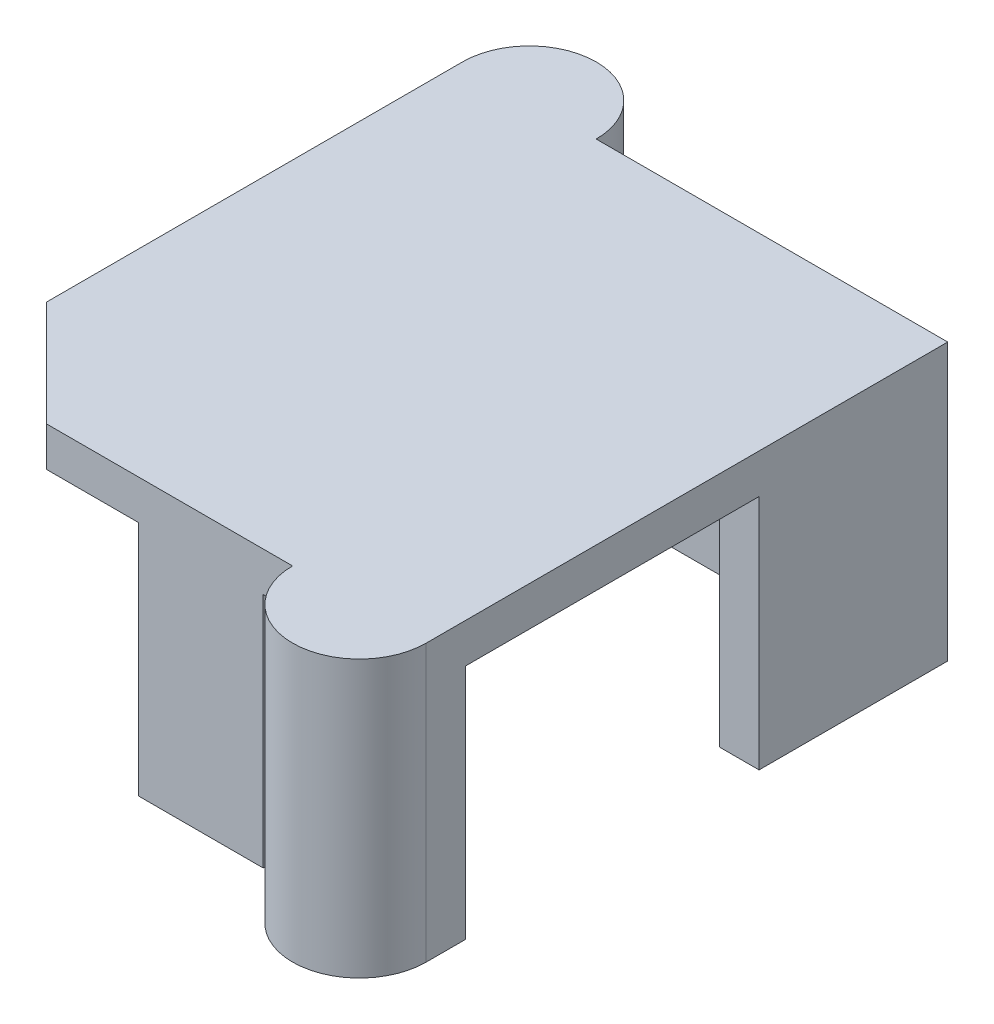
SolidWorks part; units mm, degrees
material "ABS"
ref_plane "前视基准面" through (0, 0, 0) normal (0, 0, 1) x (1, 0, 0)
ref_plane "上视基准面" through (0, 0, 0) normal (0, 1, 0) x (1, 0, 0)
ref_plane "右视基准面" through (0, 0, 0) normal (1, 0, 0) x (0, 0, -1)
sketch "草图1" plane through (0, 0, 0) normal (0, 1, 0) x (1, 0, 0)
  line L1 (-7.72, -8.41) -> (7.72, -8.41)
  line L2 (-7.72, -8.41) -> (-7.72, 8.41)
  line L3 (-7.72, 8.41) -> (7.72, 8.41)
  line L4 (7.72, -8.41) -> (7.72, 8.41)
  line L5 (-7.72, -8.41) -> (7.72, 8.41) construction
  line L6 (-7.72, 8.41) -> (7.72, -8.41) construction
  point P0 (0, 0)
  dimension "D1" = 15.44
  dimension "D2" = 16.82
extrude "凸台-拉伸1" add sketch "草图1" along normal blind 9
shell "抽壳3" thickness 1.5
sketch "草图2" plane through (0, 0, 0) normal (0, -1, 0) x (1, 0, 0)
  line L0 (9.22, 9.91) -> (9.22, -9.91) construction
  line L1 (9.22, 8.41) -> (7.72, 8.41)
  line L2 (9.22, 8.41) -> (9.22, -2.74)
  line L3 (9.22, -2.74) -> (7.72, -2.74)
  line L4 (7.72, 8.41) -> (7.72, -2.74)
  line L5 (7.72, 8.41) -> (7.72, -8.41) construction
  dimension "D1" = 11.15
extrude "切除-拉伸1" cut sketch "草图2" against normal up to surface (9 mm away) up to face at (0, 9, 0)
sketch "草图3" plane through (0, 0, 0) normal (0, -1, 0) x (1, 0, 0)
  line L0 (-7.72, -8.41) -> (-7.72, 8.41) construction
  line L1 (-9.22, 9.91) -> (-1.72, 9.91)
  line L2 (-9.22, 9.91) -> (-9.22, 1.41)
  line L3 (-9.22, 1.41) -> (-1.72, 1.41)
  line L4 (-1.72, 9.91) -> (-1.72, 1.41)
  line L5 (-7.72, 8.41) -> (9.22, 8.41) construction
  dimension "D1" = 6
  dimension "D2" = 7
extrude "切除-拉伸2" cut sketch "草图3" against normal up to surface (9 mm away) up to face at (3.0733, 9, -0.9133)
sketch "草图4" plane through (0, 0, 0) normal (0, -1, 0) x (1, 0, 0)
  line L0 (-1.72, 9.91) -> (9.22, 9.91) construction
  line L1 (3.02, 9.91) -> (4.14, 9.91)
  line L2 (3.02, 9.91) -> (3.02, 8.41)
  line L3 (3.02, 8.41) -> (4.14, 8.41)
  line L4 (4.14, 9.91) -> (4.14, 8.41)
  line L5 (-1.72, 8.41) -> (9.22, 8.41) construction
  line L7 (-11.6392, 0) -> (13.3232, 0) construction
  line L8 (4.14, -9.91) -> (4.14, -8.41)
  line L9 (3.02, -8.41) -> (4.14, -8.41)
  line L10 (3.02, -9.91) -> (3.02, -8.41)
  line L11 (3.02, -9.91) -> (4.14, -9.91)
  line L12 (7.72, -2.74) -> (7.72, -8.41) construction
  dimension "D1" = 4.7
  dimension "D2" = 1.12
extrude "切除-拉伸3" cut sketch "草图4" against normal up to surface (9 mm away) up to face at (-0.344, 9, 1.716)
chamfer "倒角1" distance 4 1 edges at (-9.22, 9.75, 9.91)
sketch "草图5" plane through (0, 0, 0) normal (0, -1, 0) x (1, 0, 0)
  line L0 (4.14, 8.41) -> (4.14, 9.91) construction
  line L1 (9.22, 9.91) -> (4.14, 9.91)
  line L2 (3.02, -9.91) -> (-9.22, -9.91) construction
  line L3 (-9.22, -9.91) -> (-9.22, 1.41) construction
  line L4 (-9.22, -9.91) -> (-4.14, -9.91)
  arc A0 (4.14, 9.91) -> (9.22, 9.91) centre (6.68, 9.91) cw
  arc A1 (-9.22, -9.91) -> (-4.14, -9.91) centre (-6.68, -9.91) ccw
  dimension "D1" = 5.08
  dimension "D2" = 5.08
extrude "凸台-拉伸2" add sketch "草图5" against normal up to surface (10.5 mm away) up to face at (-1.044, 10.5, 1.182)
hole_wizard "M1.4X0.3 螺纹孔的螺纹孔钻头1" positions "草图9" profile "草图10" hole size "M1.4X0.3" standard "GB"
sketch "草图9" plane through (0, 0, 0) normal (0, -1, 0) x (-1, 0, 0)
  line L0 (-6.68, -12.45) -> (-6.68, -8.41) construction
  line L1 (-4.14, -8.41) -> (-9.22, -8.41) construction
  line L3 (6.68, 12.45) -> (6.68, 8.41)
  line L4 (-3.02, 8.41) -> (7.72, 8.41) construction
  arc A0 (-9.22, -9.91) -> (-4.14, -9.91) centre (-6.68, -9.91) ccw construction
  arc A1 (9.22, 9.91) -> (4.14, 9.91) centre (6.68, 9.91) ccw construction
  point P0 (6.68, 10.63)
  point P3 (-6.68, -10.63)
sketch "草图10" plane through (-6.68, 0, -10.63) normal (1, 0, 0) x (0, 0, -1)
  line L0 (0, 0) -> (0, 8)
  line L1 (0, 8) -> (0.55, 7.6695)
  line L2 (0.55, 7.6695) -> (0.55, 0.025)
  line L3 (0.55, 0.025) -> (0.575, 0)
  line L5 (0.575, 0) -> (0, 0)
  line L6 (-0.55, 0.025) -> (-0.575, 0) construction
  line L10 (0, 8) -> (-0.55, 7.6695) construction
  line L11 (0, -6.35) -> (0, 107.95) construction
  dimension "孔直径" = 1.1
  dimension "孔深度" = 8
  dimension "近端锥形沉头孔直径" = 1.15
  dimension "近端锥形沉头孔角度" = 90
  dimension "导头角度" = 118
